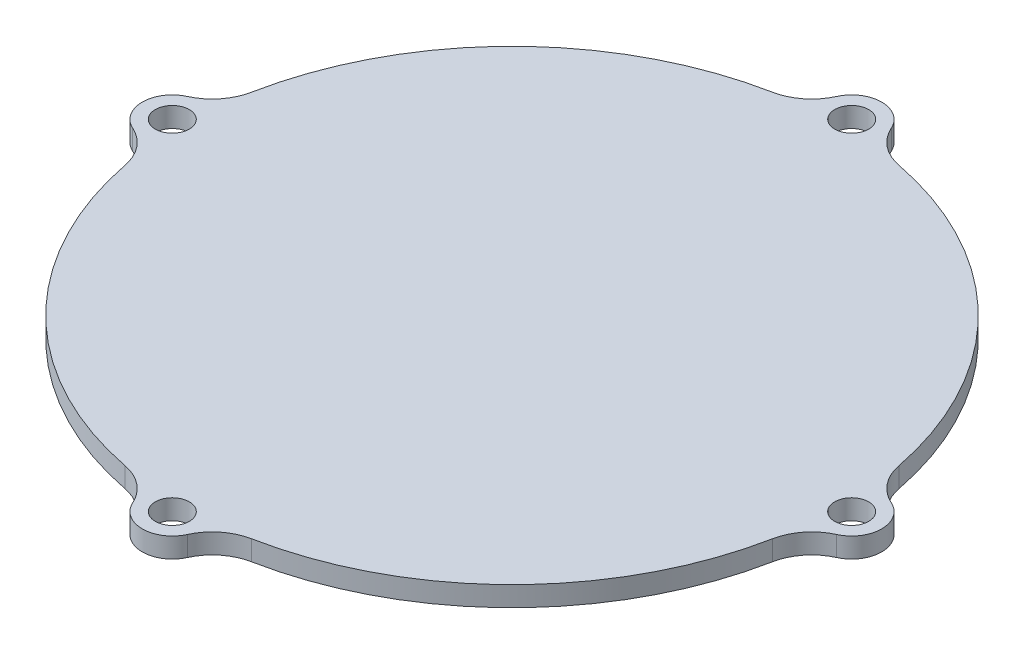
SolidWorks part; units mm, degrees
ref_plane "Front Plane" through (0, 0, 0) normal (0, 0, 1) x (1, 0, 0)
ref_plane "Top Plane" through (0, 0, 0) normal (0, 1, 0) x (1, 0, 0)
ref_plane "Right Plane" through (0, 0, 0) normal (1, 0, 0) x (0, 0, -1)
sketch "Sketch1" plane through (0, 0, 0) normal (0, 1, 0) x (1, 0, 0)
  circle A0 centre (0, 0) radius 33
  dimension "D1" = 66
extrude "Boss-Extrude1" add sketch "Sketch1" along normal blind 2
sketch "Sketch2" plane through (0, 2, 0) normal (0, 1, 0) x (1, 0, 0)
  line L0 (0, 0) -> (0, 34) construction
  circle A0 centre (0, 34) radius 3
  circle A1 centre (0, 0) radius 31 construction
  dimension "D1" = 62
  dimension "D2" = 6
extrude "Boss-Extrude2" add sketch "Sketch2" against normal through all
fillet "Fillet1" radius 5 2 edges at (2.784, 1, -32.8824) (-2.784, 1, -32.8824)
pattern_circular "CirPattern1" count 4 over 360 about axis through (0, 0, 0) along (0, 1, 0) of "Boss-Extrude2", "Fillet1"
hole_wizard "M3 Clearance Hole1" positions "Sketch5" profile "Sketch6" hole size "M3" standard "ANSI Metric" end condition through all
sketch "Sketch5" plane through (0, 2, 0) normal (0, 1, 0) x (1, 0, 0)
  point P0 (0, -34)
  point P3 (34, 0)
  point P6 (0, 34)
  point P9 (-34, 0)
sketch "Sketch6" plane through (0, 2, 34) normal (1, 0, 0) x (0, 0, 1)
  line L0 (0, 0) -> (0, 2)
  line L1 (0, 2) -> (1.7, 2)
  line L2 (1.7, 2) -> (1.7, 0)
  line L5 (1.7, 0) -> (0, 0)
  line L11 (0, -6.35) -> (0, 107.95) construction
  dimension "Thru Hole Dia." = 3.4
  dimension "Thru Hole Depth" = 2
